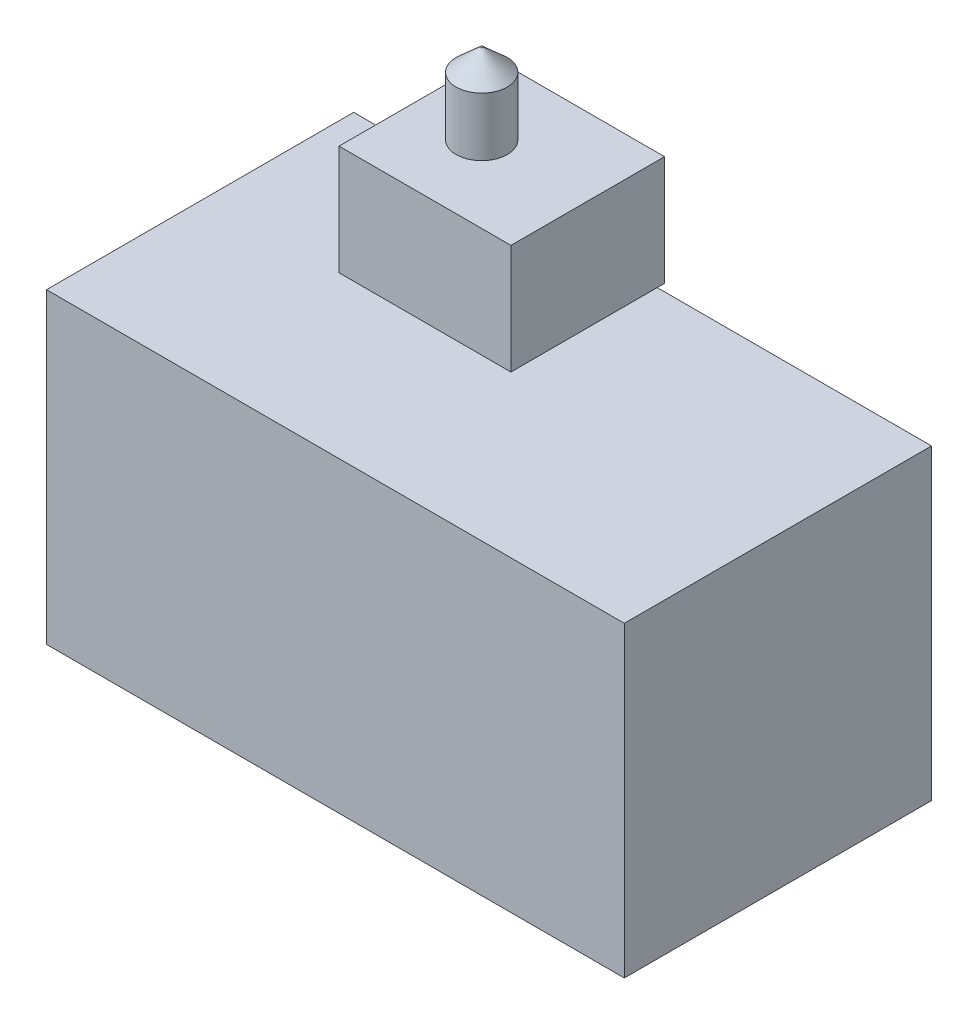
SolidWorks part; units mm, degrees
ref_plane "Plan de face" through (0, 0, 0) normal (0, 0, 1) x (1, 0, 0)
ref_plane "Plan de dessus" through (0, 0, 0) normal (0, 1, 0) x (1, 0, 0)
ref_plane "Plan de droite" through (0, 0, 0) normal (1, 0, 0) x (0, 0, -1)
sketch "Sketch1" plane through (0, 0, 0) normal (0, 0, 1) x (1, 0, 0)
  line L1 (0, 0) -> (79, 0)
  line L2 (0, 0) -> (0, 42)
  line L3 (0, 42) -> (79, 42)
  line L4 (79, 0) -> (79, 42)
  dimension "D1" = 79
  dimension "D2" = 42
extrude "Boss-Extrude1" add sketch "Sketch1" along normal blind 42 contours L3 L4 L1 L2
sketch "Sketch3" plane through (0, 42, 0) normal (0, 1, 0) x (1, 0, 0)
  line L0 (23, -4) -> (46.5, -25) construction
  line L1 (23, -4) -> (46.5, -4)
  line L2 (23, -4) -> (23, -25)
  line L3 (23, -25) -> (46.5, -25)
  line L4 (46.5, -4) -> (46.5, -25)
  line L5 (46.5, -4) -> (23, -25) construction
  line L7 (0, 0) -> (79, 0) construction
  line L8 (79, -42) -> (79, 0) construction
  point P4 (34.75, -14.5)
  dimension "D1" = 23.5
  dimension "D2" = 21
  dimension "D3" = 14.5
  dimension "D4" = 56
extrude "Boss-Extrude2" add sketch "Sketch3" along normal blind 15 from offset 5 separate body
sketch "Sketch4" plane through (0, 62, 0) normal (0, 1, 0) x (1, 0, 0)
  circle A0 centre (32, -14.5) radius 3.5
  dimension "D1" = 7
extrude "Boss-Extrude3" add sketch "Sketch4" along normal blind 8 separate body
ref_plane "Plane1" through (0, 0, 14.5) normal (0, 0, -1) x (-1, 0, 0)
sketch "Sketch5" plane through (0, 0, 14.5) normal (0, 0, -1) x (-1, 0, 0)
  line L0 (-32, 70) -> (-32, 73)
  line L1 (-28.5, 70) -> (-35.5, 70) construction
  line L2 (-32, 73) -> (-31.85, 73)
  line L3 (-31.85, 73) -> (-28.5, 70)
  line L4 (-28.5, 70) -> (-32, 70)
  dimension "D1" = 0.15
  dimension "D2" = 3
revolve "Revolve1" add sketch "Sketch5" angle 360 about L0
sketch "Sketch6" plane through (0, 42, 0) normal (0, 1, 0) x (1, 0, 0)
  circle A0 centre (32, -14.5) radius 3.5
extrude "Boss-Extrude4" add sketch "Sketch6" along normal up to surface (5 mm away) contours A0 up to face at (34.75, 47, 14.5)
